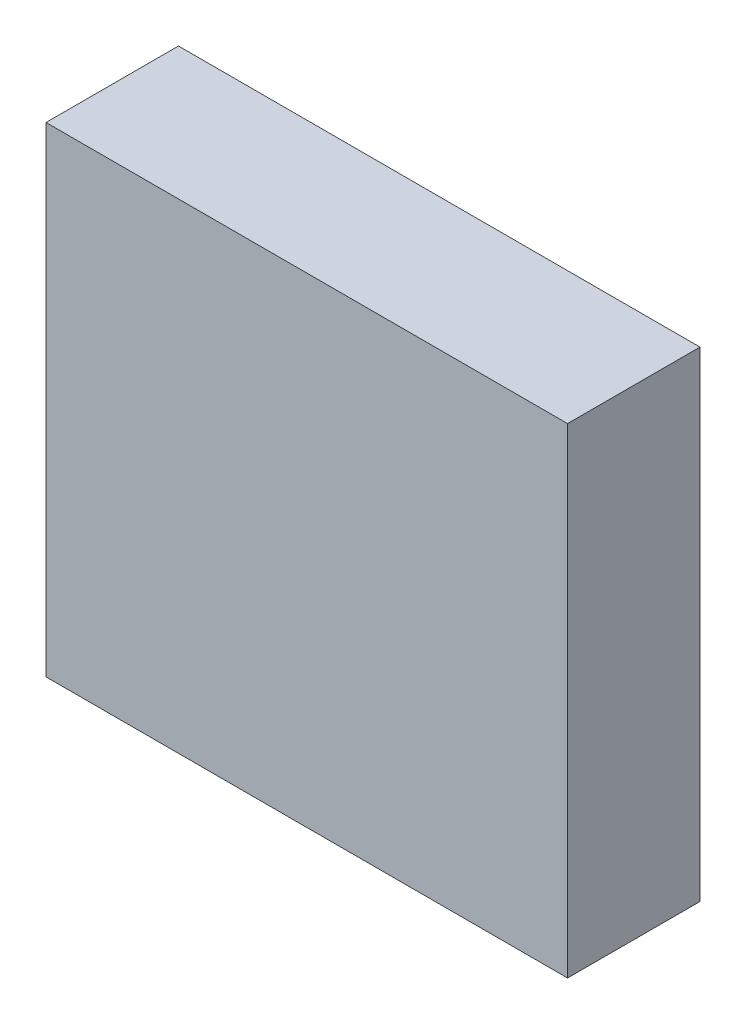
SolidWorks part; units mm, degrees
ref_plane "Front Plane" through (0, 0, 0) normal (0, 0, 1) x (1, 0, 0)
ref_plane "Top Plane" through (0, 0, 0) normal (0, 1, 0) x (1, 0, 0)
ref_plane "Right Plane" through (0, 0, 0) normal (1, 0, 0) x (0, 0, -1)
sketch "Sketch1" plane through (0, 0, 0) normal (0, 0, 1) x (1, 0, 0)
  line L0 (0, 0) -> (0, 58)
  line L1 (0, 0) -> (63, 0)
  line L2 (63, 0) -> (63, 58)
  line L3 (63, 58) -> (0, 58)
  dimension "D1" = 58
  dimension "D2" = 63
extrude "Boss-Extrude1" add sketch "Sketch1" along normal blind 16
